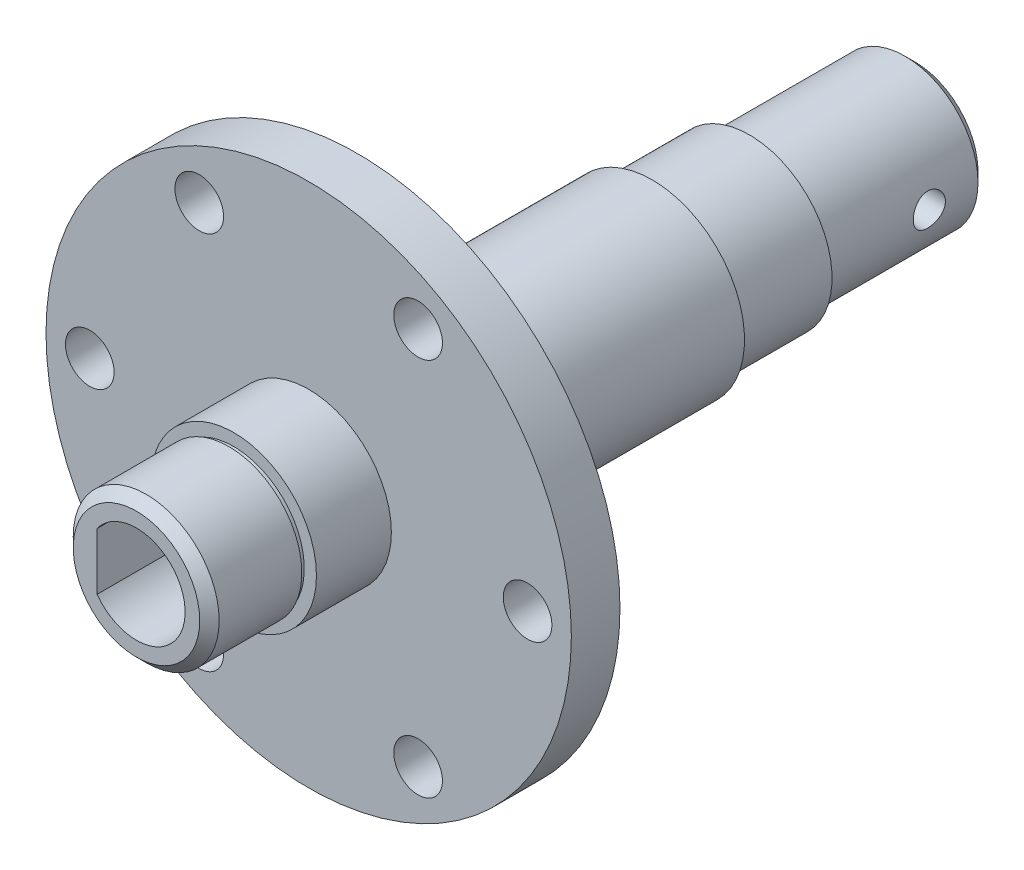
SolidWorks part; units mm, degrees
material "6061 合金"
ref_plane "前视基准面" through (0, 0, 0) normal (0, 0, 1) x (1, 0, 0)
ref_plane "上视基准面" through (0, 0, 0) normal (0, 1, 0) x (1, 0, 0)
ref_plane "右视基准面" through (0, 0, 0) normal (1, 0, 0) x (0, 0, -1)
sketch "草图1" plane through (0, 0, 0) normal (0, 0, 1) x (1, 0, 0)
  circle A0 centre (0, 0) radius 7
  dimension "D1" = 14
extrude "凸台-拉伸1" add sketch "草图1" along normal blind 54
sketch "草图2" plane through (0, 0, 54) normal (0, 0, 1) x (1, 0, 0)
  circle A0 centre (0, 0) radius 5
  dimension "D1" = 10
extrude "凸台-拉伸2" add sketch "草图2" along normal blind 7
chamfer "倒角1" distance 1 angle 45 1 edges at (5, 0, 61)
ref_plane "基准面1" through (0, 0, 42) normal (0, 0, 1) x (1, 0, 0)
sketch "草图3" plane through (0, 0, 42) normal (0, 0, 1) x (1, 0, 0)
  circle A0 centre (0, 0) radius 10
  dimension "D1" = 20
extrude "凸台-拉伸3" add sketch "草图3" against normal blind 2
sketch "草图4" plane through (0, 0, 0) normal (0, 0, -1) x (-1, 0, 0)
  circle A0 centre (0, 0) radius 6
  dimension "D1" = 12
extrude "凸台-拉伸4" add sketch "草图4" along normal blind 25
sketch "草图7" plane through (0, 0, 42) normal (0, 0, 1) x (1, 0, 0)
  circle A1 centre (0, 0) radius 10
  circle A2 centre (0, 0) radius 10
  dimension "D1" = 0
extrude "凸台-拉伸5" add sketch "草图7" along normal blind 4.3
sketch "草图9" plane through (0, 0, 40) normal (0, 0, -1) x (-1, 0, 0)
  circle A0 centre (0, 0) radius 6
  circle A1 centre (0, 0) radius 10
  circle A2 centre (0, 0) radius 10
  dimension "D2" = 12
  dimension "D1" = 0
extrude "切除-拉伸3" cut sketch "草图9" against normal blind 1.3
sketch "草图11" plane through (0, 0, 46.3) normal (0, 0, 1) x (1, 0, 0)
  circle A0 centre (0, 0) radius 27
  circle A1 centre (0, 0) radius 10
  circle A2 centre (0, 0) radius 10
  dimension "D2" = 54
  dimension "D1" = 0
extrude "凸台-拉伸6" add sketch "草图11" against normal blind 5
sketch "草图12" plane through (0, 0, 41.3) normal (0, 0, -1) x (-1, 0, 0)
  circle A0 centre (0, 0) radius 6
  circle A1 centre (0, 0) radius 9.5
  dimension "D1" = 12
  dimension "D2" = 19
extrude "凸台-拉伸7" add sketch "草图12" along normal blind 30
sketch "草图13" plane through (0, 0, -25) normal (0, 0, -1) x (-1, 0, 0)
  line L0 (0, -3) -> (0, 3) construction
  line L1 (2.15, 2.0922) -> (2.15, -2.0922)
  line L2 (-2.15, 2.0922) -> (-2.15, -2.0922)
  arc A0 (-2.15, -2.0922) -> (2.15, -2.0922) centre (0, 0) ccw
  arc A1 (2.15, 2.0922) -> (-2.15, 2.0922) centre (0, 0) ccw
  dimension "D1" = 6
  dimension "D2" = 2.15
sketch "草图14" plane through (0, 0, 46.3) normal (0, 0, 1) x (1, 0, 0)
  circle A0 centre (0, 0) radius 22.5 construction
  circle A1 centre (22.5, 0) radius 2.5
  circle A2 centre (11.25, -19.4856) radius 2.5
  circle A3 centre (-11.25, -19.4856) radius 2.5
  circle A4 centre (-22.5, 0) radius 2.5
  circle A5 centre (-11.25, 19.4856) radius 2.5
  circle A6 centre (11.25, 19.4856) radius 2.5
  point P17 (0, 0)
  dimension "D1" = 45
  dimension "D2" = 5
  dimension "D3" = 6
extrude "切除-拉伸4" cut sketch "草图14" against normal blind 10
extrude "切除-拉伸5" cut sketch "草图13" against normal blind 30
chamfer "倒角2" distance 1 angle 45 1 edges at (-6, 0, -25)
ref_plane "基准面2" through (7.85, 0, 0) normal (1, 0, 0) x (0, 0, -1)
sketch "草图15" plane through (7.85, 0, 0) normal (1, 0, 0) x (0, 0, -1)
  line L0 (25, 0) -> (0, 0) construction
  line L1 (25, -5) -> (25, 5) construction
  point P5 (17, 0)
  dimension "D1" = 8
hole_wizard "M3 螺纹孔1" positions "3D草图1" profile "草图16" tap size "M3" standard "GB"
sketch3d "3D草图1"
  point P0 (7.85, 0, -17)
sketch "草图16" plane through (7.85, 0, -17) normal (0, 1, 0) x (0, 0, -1)
  line L0 (0, 0) -> (0, 19.2511)
  line L1 (0, 19.2511) -> (1.25, 18.5)
  line L2 (1.25, 18.5) -> (1.25, 0)
  line L5 (1.25, 0) -> (0, 0)
  line L10 (0, 19.2511) -> (-1.25, 18.5) construction
  line L11 (0, -6.35) -> (0, 107.95) construction
  dimension "螺纹孔钻头直径" = 2.5
  dimension "螺纹孔钻头深度" = 18.5
  dimension "导头角度" = 118
cosmetic thread "孔螺蚊线1" [suppressed] parameters "D1"=13.9, "D2"=3
sketch "草图22" plane through (0, 0, 0) normal (1, 0, 0) x (0, 0, -1)
  line L1 (-11.3, -9.6076) -> (27.1711, -9.6076)
  line L2 (-11.3, -9.6076) -> (-11.3, 15.0957)
  line L3 (-11.3, 15.0957) -> (27.1711, 15.0957)
  line L4 (27.1711, -9.6076) -> (27.1711, 15.0957)
extrude "切除-拉伸10" cut sketch "草图22" against normal through all both and the other way through all
sketch "草图24" plane through (0, 0, 11.3) normal (0, 0, -1) x (-1, 0, 0)
  circle A0 centre (0, 0) radius 9.5
extrude "凸台-拉伸9" add sketch "草图24" along normal blind 10.3
sketch "草图25" plane through (0, 0, 1) normal (0, 0, -1) x (-1, 0, 0)
  circle A0 centre (0, 0) radius 7.5
  dimension "D1" = 15
extrude "凸台-拉伸10" add sketch "草图25" along normal blind 17
sketch "草图26" plane through (0, 0, 0) normal (1, 0, 0) x (0, 0, -1)
  line L0 (-46.3, 27) -> (-46.3, -27) construction
  line L1 (-46.3, -7.4103) -> (-66.1704, -7.4103)
  line L2 (-46.3, -7.4103) -> (-46.3, 9.9233)
  line L3 (-46.3, 9.9233) -> (-66.1704, 9.9233)
  line L4 (-66.1704, -7.4103) -> (-66.1704, 9.9233)
extrude "切除-拉伸11" cut sketch "草图26" against normal through all both and the other way through all
sketch "草图27" plane through (0, 0, 46.3) normal (0, 0, 1) x (1, 0, 0)
  circle A0 centre (0, 0) radius 9.5
  dimension "D1" = 19
extrude "凸台-拉伸11" add sketch "草图27" along normal blind 7.7
sketch "草图29" plane through (0, 0, 54) normal (0, 0, 1) x (1, 0, 0)
  circle A0 centre (0, 0) radius 7.5
  dimension "D1" = 15
extrude "凸台-拉伸12" add sketch "草图29" along normal blind 10
sketch "草图30" plane through (0, 0, -16) normal (0, 0, -1) x (-1, 0, 0)
  line L0 (4.05, 2.9321) -> (4.05, -2.9321)
  arc A0 (4.05, 2.9321) -> (4.05, -2.9321) centre (0, 0) ccw
  dimension "D1" = 10
  dimension "D2" = 4.05
extrude "切除-拉伸12" cut sketch "草图30" against normal up to next
ref_plane "基准面3" through (-9.5, 0, 0) normal (-1, 0, 0) x (0, 0, 1)
hole_wizard "M4 螺纹孔1" positions "草图32" profile "草图31" tap size "M4" standard "GB" end condition through all
sketch "草图32" plane through (-9.5, 0, 0) normal (-1, 0, 0) x (0, 0, 1)
  line L0 (-16, 7.5) -> (-16, -7.5) construction
  point P0 (-10, 0)
  dimension "D1" = 6
sketch "草图31" plane through (-9.5, 0, -10) normal (0, 1, 0) x (0, 0, 1)
  line L0 (0, 0) -> (0, 36.5)
  line L1 (0, 36.5) -> (1.65, 36.5)
  line L2 (1.65, 36.5) -> (1.65, 0)
  line L5 (1.65, 0) -> (0, 0)
  line L11 (0, -6.35) -> (0, 107.95) construction
  dimension "通孔螺纹孔钻头直径" = 3.3
  dimension "通孔螺纹孔钻头深度" = 36.5
cosmetic thread "孔螺蚊线2" parameters "D2"=4
chamfer "倒角4" distance 1 angle 45 2 edges at (-7.5, 0, -16) (7.5, 0, 64)
sketch "草图33" plane through (0, 0, 1) normal (0, 0, -1) x (-1, 0, 0)
  circle A0 centre (0, 0) radius 9.5
  circle A1 centre (0, 0) radius 8.5
  dimension "D1" = 17
extrude "切除-拉伸13" cut sketch "草图33" against normal blind 10
sketch "草图34" plane through (0, 0, 54) normal (0, 0, 1) x (1, 0, 0)
  circle A0 centre (0, 0) radius 9.5
  circle A1 centre (0, 0) radius 8.5
  dimension "D1" = 17
extrude "切除-拉伸14" cut sketch "草图34" against normal blind 7.7
sketch "草图35" plane through (0, 0, 0) normal (0, 1, 0) x (1, 0, 0)
  line L0 (0, -1) -> (0, 6.2256) construction
  line L1 (8.5, -1) -> (-8.5, -1) construction
  line L2 (7.5, -1) -> (7.5, -0.5)
  line L3 (7.5, -1) -> (7.5, 8.35) construction
  line L4 (7.5, -0.5) -> (7.25, -0.5)
  line L5 (7.25, -0.5) -> (7.25, -1)
  line L6 (7.25, -1) -> (7.5, -1)
  dimension "D1" = 0.5
  dimension "D2" = 0.25
revolve "切除-旋转1" cut sketch "草图35" angle 360 about L0
sketch "草图36" plane through (0, 0, 0) normal (0, 1, 0) x (1, 0, 0)
  line L0 (0, -54) -> (0, -66.3322) construction
  line L1 (-7.5, -54) -> (7.5, -54) construction
  line L2 (7.5, -54) -> (7.25, -54)
  line L3 (7.25, -54) -> (7.25, -54.5)
  line L4 (7.25, -54.5) -> (7.5, -54.5)
  line L5 (7.5, -63) -> (7.5, -54) construction
  line L6 (7.5, -54.5) -> (7.5, -54)
  dimension "D1" = 0.5
  dimension "D2" = 0.25
revolve "切除-旋转2" cut sketch "草图36" angle 360 about L0
